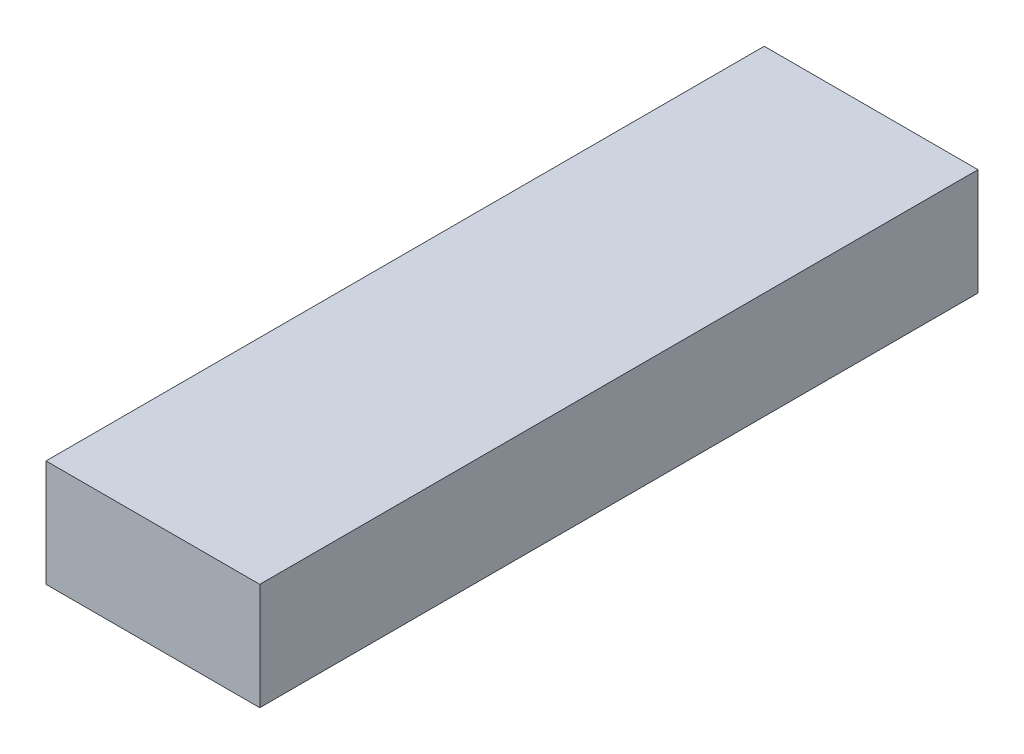
SolidWorks part; units mm, degrees
ref_plane "Front Plane" through (0, 0, 0) normal (0, 0, 1) x (1, 0, 0)
ref_plane "Top Plane" through (0, 0, 0) normal (0, 1, 0) x (1, 0, 0)
ref_plane "Right Plane" through (0, 0, 0) normal (1, 0, 0) x (0, 0, -1)
sketch "Sketch1" plane through (0, 0, 0) normal (0, 1, 0) x (1, 0, 0)
  line L0 (-3.3783, 4.8671) -> (-3.3783, -16.4689)
  line L1 (-3.3783, -16.4689) -> (2.9717, -16.4689)
  line L2 (2.9717, -16.4689) -> (2.9717, 4.8671)
  line L3 (2.9717, 4.8671) -> (-3.3783, 4.8671)
  dimension "D1" = 21.336
  dimension "D2" = 6.35
extrude "Boss-Extrude1" add sketch "Sketch1" along normal blind 3.175
